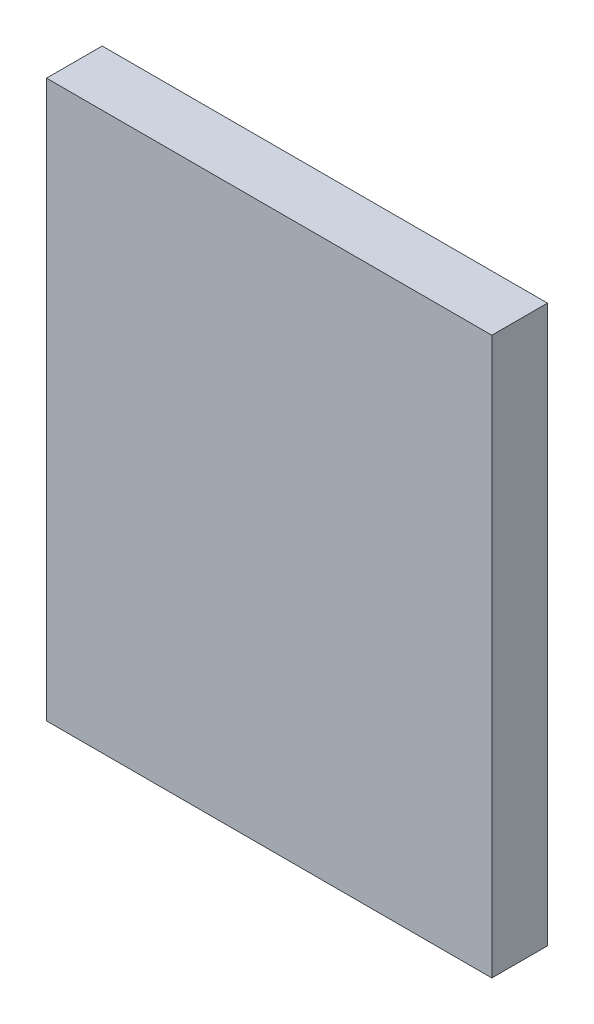
SolidWorks part; units mm, degrees
material "Cedar"
ref_plane "Front Plane" through (0, 0, 0) normal (0, 0, 1) x (1, 0, 0)
ref_plane "Top Plane" through (0, 0, 0) normal (0, 1, 0) x (1, 0, 0)
ref_plane "Right Plane" through (0, 0, 0) normal (1, 0, 0) x (0, 0, -1)
sketch "Sketch1" plane through (0, 0, 0) normal (0, 0, 1) x (1, 0, 0)
  line L1 (-12, -15) -> (12, -15)
  line L2 (-12, -15) -> (-12, 15)
  line L3 (-12, 15) -> (12, 15)
  line L4 (12, -15) -> (12, 15)
  line L5 (-12, -15) -> (12, 15) construction
  line L6 (-12, 15) -> (12, -15) construction
  point P0 (0, 0)
  dimension "D1" = 24
  dimension "D2" = 30
extrude "Boss-Extrude1" add sketch "Sketch1" along normal blind 3
